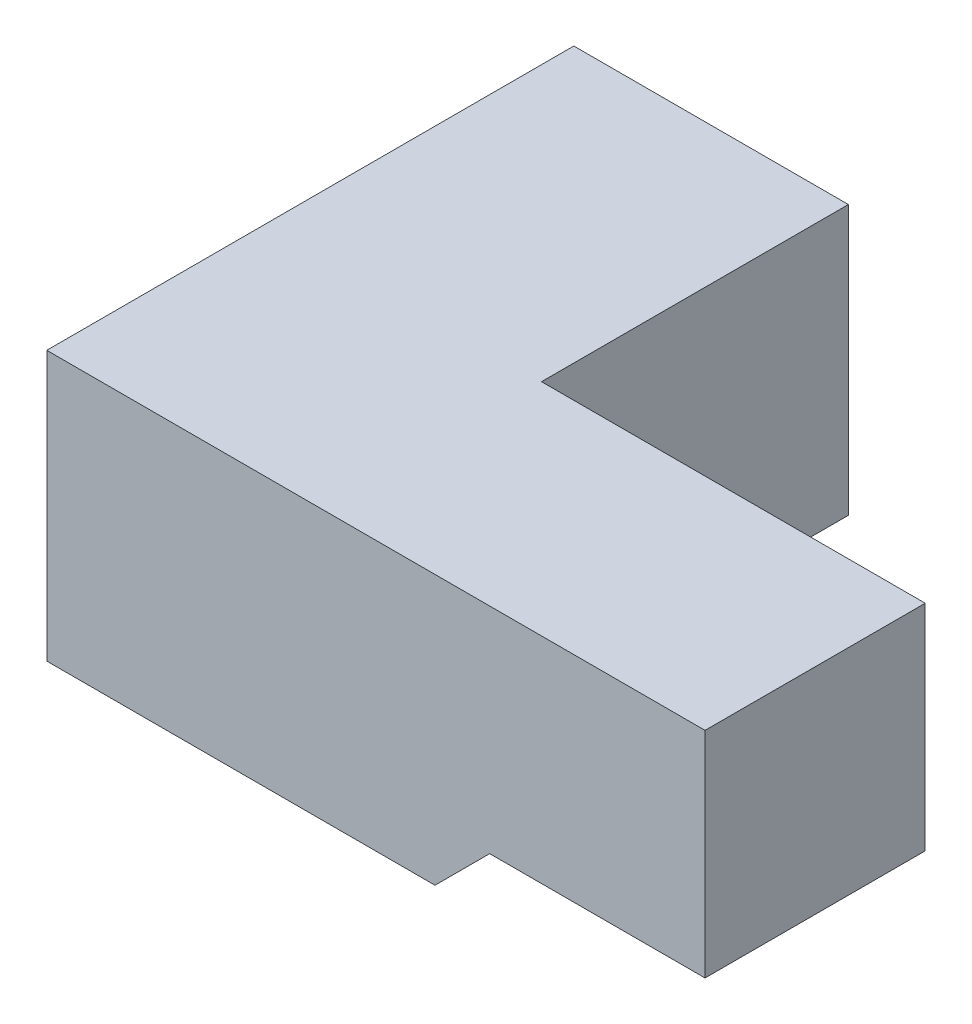
SolidWorks part; units mm, degrees
material "1.4301 2J EF"
ref_plane "Ebene vorne" through (0, 0, 0) normal (0, 0, 1) x (1, 0, 0)
ref_plane "Ebene oben" through (0, 0, 0) normal (0, 1, 0) x (1, 0, 0)
ref_plane "Ebene rechts" through (0, 0, 0) normal (1, 0, 0) x (0, 0, -1)
sketch "Skizze1" plane through (0, 0, 0) normal (0, 0, 1) x (1, 0, 0)
  line L0 (-255, -250) -> (255, -250) construction
  line L1 (255, 250) -> (-255, 250)
  line L2 (255, 250) -> (255, -250)
  line L3 (255, -250) -> (-255, -250)
  line L4 (-255, 250) -> (-255, -250)
  line L5 (255, 250) -> (-255, -250) construction
  line L6 (255, -250) -> (-255, 250) construction
  line L7 (255, -250) -> (255, 250) construction
  point P0 (0, 0)
  point P11 (0, 0)
sketch3d "3D-Skizze1"
  line L0 (0, 0, 0) -> (0, 0, 774.5) construction
  line L1 (0, 0, 774.5) -> (516.95, 0, 774.5) construction
  line L2 (516.95, 0, 774.5) -> (567.75, 50.8, 774.5) construction
  line L3 (567.75, 50.8, 774.5) -> (967.75, 50.8, 774.5) construction
  line L4 (255, 250, 0) -> (255, 250, 570)
  line L5 (255, 250, 570) -> (967.75, 250, 570)
  line L6 (-255, 250, 0) -> (-255, 250, 979)
  line L7 (-255, 250, 979) -> (967.75, 250, 979)
  line L8 (967.75, -148.4, 570) -> (567.75, -148.4, 570)
  line L9 (255, -250, 0) -> (255, -250, 570)
  line L10 (255, -250, 570) -> (466.15, -250, 570)
  line L11 (967.75, -148.4, 979) -> (567.75, -148.4, 979)
  line L12 (-255, -250, 0) -> (-255, -250, 979)
  line L13 (-255, -250, 979) -> (466.15, -250, 979)
  line L14 (466.15, -250, 979) -> (567.75, -148.4, 979)
  line L15 (466.15, -250, 570) -> (567.75, -148.4, 570)
  line L16 (-255, 250, 979) -> (-255, -250, 979)
  line L17 (255, 250, 570) -> (255, -250, 570)
  dimension "D1" = 774.5
  dimension "D2" = 45
  dimension "D3" = 400
  dimension "D4" = 400
  dimension "D5" = 570
  dimension "D7" = 979
  dimension "D6" = 400
  dimension "D8" = 45
  dimension "D9" = 45
sketch "Skizze6" plane through (967.75, 0, 0) normal (-1, 0, 0) x (0, 0, 1)
  line L0 (570, -148.4) -> (979, -148.4) construction
  line L1 (979, 250) -> (570, 250)
  line L2 (979, 250) -> (979, -148.4)
  line L3 (979, -148.4) -> (570, -148.4)
  line L4 (570, 250) -> (570, -148.4)
  line L5 (979, 250) -> (570, -148.4) construction
  line L6 (979, -148.4) -> (570, 250) construction
  line L7 (979, 250) -> (979, -148.4) construction
  point P0 (774.5, 50.8)
sketch "Skizze7" plane through (0, 0, 0) normal (0, 0, 1) x (1, 0, 0)
  line L1 (-255, 250) -> (255, 250)
  line L2 (-255, 250) -> (-255, -250)
  line L3 (-255, -250) -> (255, -250)
  line L4 (255, 250) -> (255, -250)
extrude "Aufsatz-Linear austragen1" add sketch "Skizze7" along normal up to vertex (979 mm away)
sketch "Skizze8" plane through (-255, 0, 0) normal (-1, 0, 0) x (0, 0, 1)
  line L1 (570, -148.4) -> (979, -148.4)
  line L2 (570, -148.4) -> (570, 250)
  line L3 (570, 250) -> (979, 250)
  line L4 (979, -148.4) -> (979, 250)
extrude "Aufsatz-Linear austragen2" add sketch "Skizze8" against normal up to vertex (1222.75 mm away)
sketch "Skizze9" plane through (-255, 0, 0) normal (-1, 0, 0) x (0, 0, 1)
  line L1 (570, 250) -> (979, 250)
  line L2 (570, 250) -> (570, -250)
  line L3 (570, -250) -> (979, -250)
  line L4 (979, 250) -> (979, -250)
extrude "Aufsatz-Linear austragen3" add sketch "Skizze9" against normal up to vertex (721.15 mm away)
draft "Formschräge1" type of draft neutral plane draft angle 45 faces to draft 1 face at (466.15, -199.2, 774.5) neutral plane through (-255, -250, 979) neutral plane normal (0, -1, 0) parameters "D1"=45
